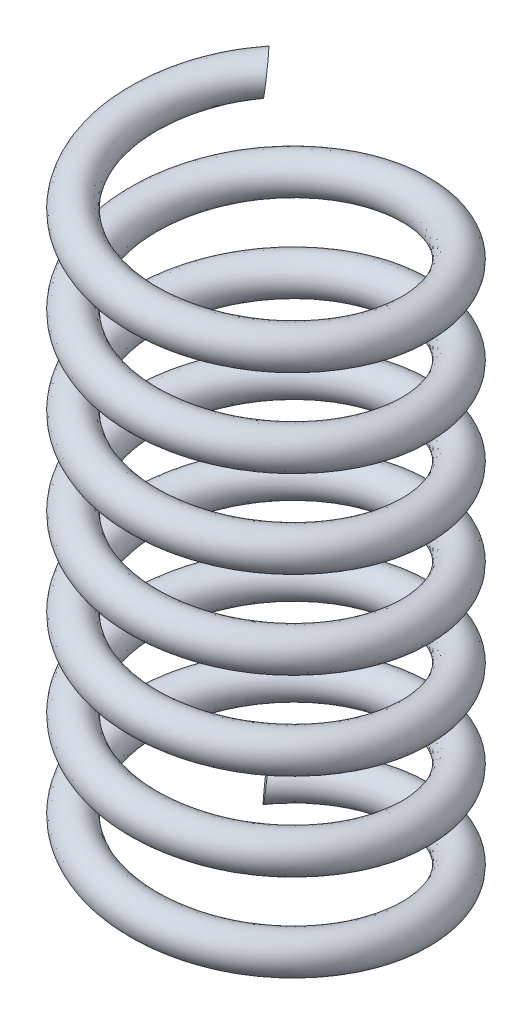
SolidWorks part; units mm, degrees
ref_plane "Front Plane" through (0, 0, 0) normal (0, 0, 1) x (1, 0, 0)
ref_plane "Top Plane" through (0, 0, 0) normal (0, 1, 0) x (1, 0, 0)
ref_plane "Right Plane" through (0, 0, 0) normal (1, 0, 0) x (0, 0, -1)
sketch "Sketch1" plane through (0, 0, 0) normal (0, 1, 0) x (1, 0, 0)
  circle A0 centre (0, 0) radius 2.3241
  dimension "D1" = 4.6482
curve "Helix/Spiral1" pitch 1.4877 height 10.414 turns 7
ref_plane "Plane1" through (-1.6434, 10.414, -1.6434) normal (0.7035, 0.1014, -0.7035) x (-0.6963, -0.1001, -0.7107)
sketch "Sketch2" plane through (-1.6434, 10.414, -1.6434) normal (0.7035, 0.1014, -0.7035) x (-0.6963, -0.1001, -0.7107)
  circle A0 centre (-4.5473, -1.2192) radius 0.3175
  dimension "D1" = 0.635
sweep "Sweep1" add profiles "Sketch2" path "Helix/Spiral1"
